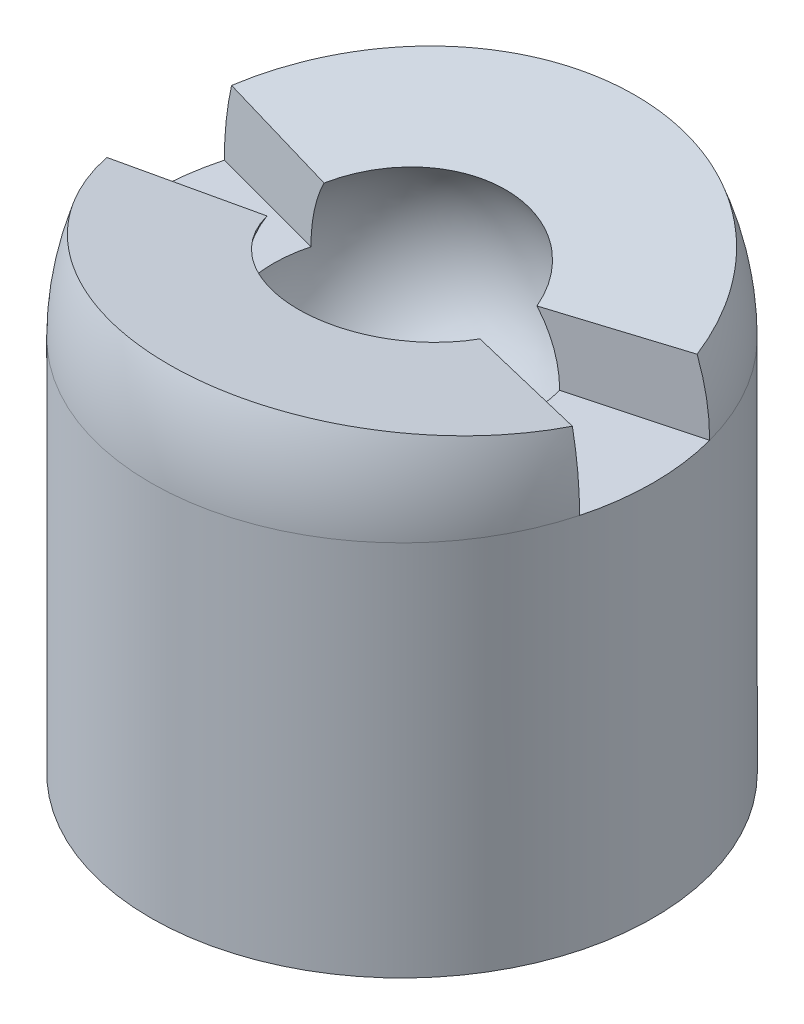
SolidWorks part; units mm, degrees
ref_plane "Front Plane" through (0, 0, 0) normal (0, 0, 1) x (1, 0, 0)
ref_plane "Top Plane" through (0, 0, 0) normal (0, 1, 0) x (1, 0, 0)
ref_plane "Right Plane" through (0, 0, 0) normal (1, 0, 0) x (0, 0, -1)
sketch "Sketch1" plane through (0, 0, 0) normal (0, 1, 0) x (1, 0, 0)
  circle A0 centre (0, 0) radius 4
  dimension "D1" = 8
extrude "Boss-Extrude1" add sketch "Sketch1" along normal blind 10
fillet "Fillet2" radius 4 1 edges at (0, 10, 4)
sketch "Sketch2" plane through (0, 0, 0) normal (1, 0, 0) x (0, 0, -1)
  line L0 (4, 6) -> (-4, 6) construction
  line L1 (-2.05, 6) -> (2.05, 6)
  arc A0 (-2.05, 6) -> (2.05, 6) centre (0, 6) ccw
  dimension "D1" = 4.1
revolve "Cut-Revolve1" cut sketch "Sketch2" angle 360 about L1
sketch "Sketch3" plane through (0, 0, 0) normal (1, 0, 0) x (0, 0, -1)
  line L0 (0, 6) -> (0, 7) construction
  line L1 (4, 6) -> (-4, 6) construction
  line L2 (0, 4.4) -> (0, -4.4) construction
  line L3 (0, 7) -> (24.0216, 10.1625)
  line L4 (24.0216, 10.1625) -> (-24.0216, 10.1625)
  line L5 (-24.0216, 10.1625) -> (0, 7)
  dimension "D1" = 1
  dimension "D2" = 97.5
  dimension "D3" = 97.5
extrude "Cut-Extrude1" cut sketch "Sketch3" against normal mid plane 15
ref_plane "Plane1" through (0, 6, 0) normal (0, 1, 0) x (1, 0, 0)
sketch "Sketch4" plane through (0, 6, 0) normal (0, 1, 0) x (1, 0, 0)
  line L1 (-0.5574, 0.1494) -> (-6.8908, 1.8464)
  line L2 (-6.8908, 1.8464) -> (-6.8908, -1.8464)
  line L3 (-6.8908, -1.8464) -> (-0.5574, -0.1494)
  line L4 (7.8613, 2.1064) -> (7.8613, -2.1064)
  line L5 (7.8613, -2.1064) -> (0.6143, -0.1646)
  line L6 (-4.3657, 0) -> (4.3657, 0) construction
  line L7 (0.6143, 0.1646) -> (7.8613, 2.1064)
  line L9 (-0.5574, 0.1494) -> (-0.5574, -0.1494)
  line L11 (0.6143, 0.1646) -> (0.6143, -0.1646)
  dimension "D1" = 15
  dimension "D2" = 15
  dimension "D3" = 15
extrude "Cut-Extrude2" cut sketch "Sketch4" along normal blind 15
